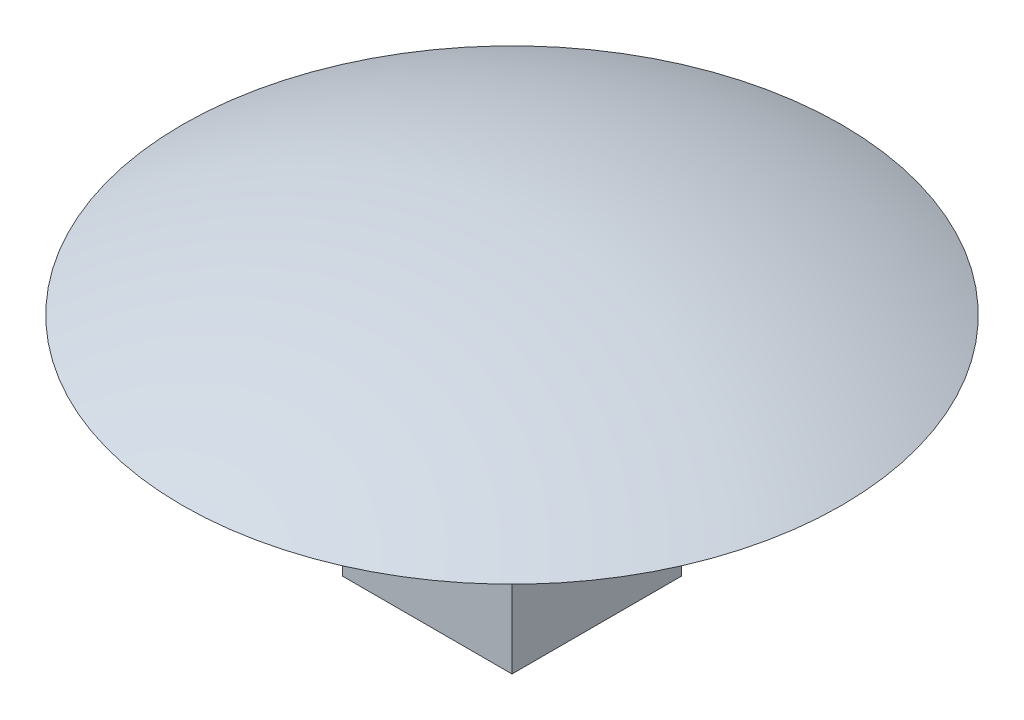
SolidWorks part; units mm, degrees
ref_plane "Front Plane" through (0, 0, 0) normal (0, 0, 1) x (1, 0, 0)
ref_plane "Top Plane" through (0, 0, 0) normal (0, 1, 0) x (1, 0, 0)
ref_plane "Right Plane" through (0, 0, 0) normal (1, 0, 0) x (0, 0, -1)
sketch "Sketch1" plane through (0, 0, 0) normal (0, 0, 1) x (1, 0, 0)
  line L0 (0, 0) -> (0, 11.1007) construction
  line L1 (0, 0) -> (0, 2)
  line L2 (0, 0) -> (8.75, 0)
  arc A0 (8.75, 0) -> (0, 2) centre (0, -18.1406) ccw
  dimension "D1" = 2
  dimension "D2" = 17.5
revolve "Revolve1" add sketch "Sketch1" angle 360 about L0
sketch "Sketch2" plane through (0, 0, 0) normal (0, -1, 0) x (1, 0, 0)
  line L0 (-2.25, 2.25) -> (2.25, -2.25) construction
  line L1 (-2.25, 2.25) -> (2.25, 2.25)
  line L2 (-2.25, 2.25) -> (-2.25, -2.25)
  line L3 (-2.25, -2.25) -> (2.25, -2.25)
  line L4 (2.25, 2.25) -> (2.25, -2.25)
  dimension "D1" = 4.5
extrude "Extrude1" add sketch "Sketch2" along normal blind 6
